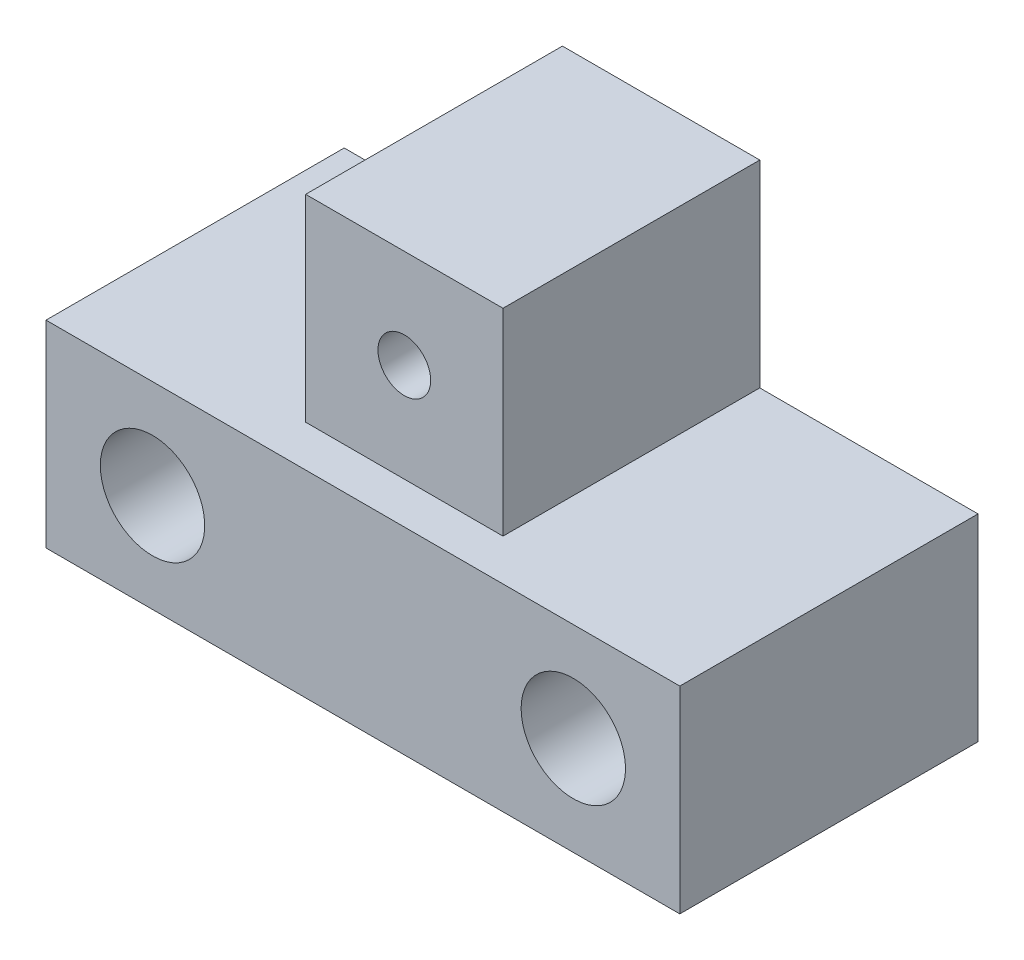
SolidWorks part; units mm, degrees
ref_plane "Front Plane" through (0, 0, 0) normal (0, 0, 1) x (1, 0, 0)
ref_plane "Top Plane" through (0, 0, 0) normal (0, 1, 0) x (1, 0, 0)
ref_plane "Right Plane" through (0, 0, 0) normal (1, 0, 0) x (0, 0, -1)
sketch "Sketch1" plane through (0, 0, 0) normal (0, 0, 1) x (1, 0, 0)
  line L0 (0, 0) -> (0, 5.9566)
  line L1 (0, 5.9566) -> (6.5867, 5.9566)
  line L2 (6.5867, 5.9566) -> (6.5867, 11.9131)
  line L3 (6.5867, 11.9131) -> (12.5433, 11.9131)
  line L4 (12.5433, 11.9131) -> (12.5433, 5.9566)
  line L5 (12.5433, 5.9566) -> (19.13, 5.9566)
  line L6 (19.13, 5.9566) -> (19.13, 0)
  line L7 (19.13, 0) -> (0, 0)
  line L8 (12.5433, 11.9131) -> (6.5867, 5.9566) construction
  line L10 (6.5867, 11.9131) -> (12.5433, 5.9566) construction
  circle A0 centre (9.565, 8.9349) radius 0.795
  dimension "D1" = 1.59
  dimension "D2" = 5.9566
  dimension "D3" = 19.13
extrude "Boss-Extrude1" add sketch "Sketch1" along normal blind 9
sketch "Sketch4" plane through (12.5433, 0, 0) normal (1, 0, 0) x (0, 0, -1)
  line L0 (-9, 11.9131) -> (0, 11.9131) construction
  line L1 (-9, 5.9566) -> (-7.75, 5.9566)
  line L2 (-9, 5.9566) -> (-9, 11.9131)
  line L3 (-9, 11.9131) -> (-7.75, 11.9131)
  line L4 (-7.75, 5.9566) -> (-7.75, 11.9131)
  dimension "D1" = 1.25
extrude "Cut-Extrude2" cut sketch "Sketch4" against normal through all
sketch "Sketch5" plane through (0, 0, 0) normal (0, 0, -1) x (-1, 0, 0)
  line L0 (-15.915, 2.9783) -> (-15.915, 5.9566) construction
  line L1 (-19.13, 5.9566) -> (-12.5433, 5.9566) construction
  line L2 (-15.915, 0) -> (-15.915, 2.9783) construction
  line L3 (0, 0) -> (-19.13, 0) construction
  line L4 (-15.915, 2.9783) -> (-19.13, 2.9783) construction
  line L5 (-19.13, 0) -> (-19.13, 5.9566) construction
  line L6 (-3.215, 2.9783) -> (0, 2.9783) construction
  line L7 (0, 5.9566) -> (0, 0) construction
  circle A0 centre (-3.215, 2.9783) radius 1.575
  circle A1 centre (-15.915, 2.9783) radius 1.575
  dimension "D1" = 3.15
  dimension "D2" = 12.7
extrude "Cut-Extrude3" cut sketch "Sketch5" against normal through all
